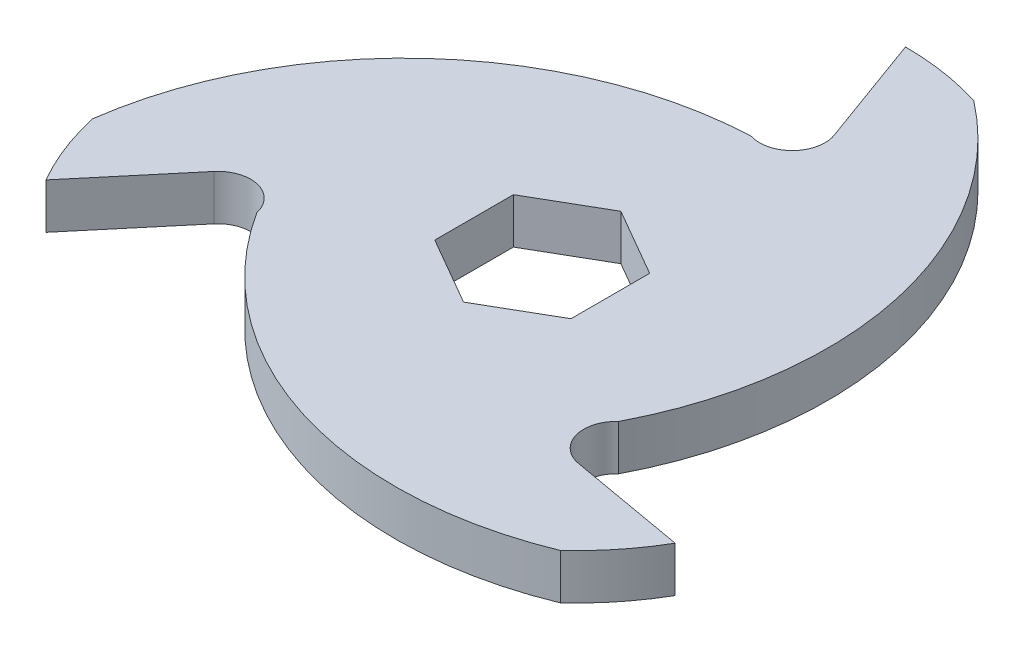
SolidWorks part; units mm, degrees
ref_plane "Front Plane" through (0, 0, 0) normal (0, 0, 1) x (1, 0, 0)
ref_plane "Top Plane" through (0, 0, 0) normal (0, 1, 0) x (1, 0, 0)
ref_plane "Right Plane" through (0, 0, 0) normal (1, 0, 0) x (0, 0, -1)
sketch "Sketch2" plane through (0, 0, 0) normal (0, 1, 0) x (1, 0, 0)
  line L0 (0, 50.8) -> (0, 0) construction
  line L1 (0, 0) -> (-43.9941, -25.4) construction
  line L2 (0, 0) -> (43.9941, -25.4) construction
  line L3 (0, 50.8) -> (5.6992, 35.1416)
  line L4 (43.9941, -25.4) -> (27.5839, -22.5064)
  line L5 (-43.9941, -25.4) -> (-33.2831, -12.6352)
  line L7 (0, 10.9985) -> (-9.525, 5.4993)
  line L8 (-9.525, 5.4993) -> (-9.525, -5.4993)
  line L9 (-9.525, -5.4993) -> (0, -10.9985)
  line L10 (0, -10.9985) -> (9.525, -5.4993)
  line L11 (9.525, -5.4993) -> (9.525, 5.4993)
  line L12 (9.525, 5.4993) -> (0, 10.9985)
  circle A0 centre (0, 0) radius 50.8 construction
  circle A1 centre (0, 13.2055) radius 37.5945
  circle A2 centre (11.4363, -6.6028) radius 37.5945
  circle A3 centre (-11.4363, -6.6028) radius 37.5945
  arc A4 (5.6992, 35.1416) -> (0, 29.21) centre (1.3938, 33.5746) cw
  arc A5 (27.5839, -22.5064) -> (25.2966, -14.605) centre (28.3796, -17.9943) cw
  arc A6 (-33.2831, -12.6352) -> (-25.2966, -14.605) centre (-29.7733, -15.5803) cw
  circle A7 centre (0, 0) radius 9.525 construction
  point P15 (0, 0)
  point P25 (0, 0)
  point P31 (0, 0)
  point P32 (0, 0)
  dimension "D1" = 101.6
  dimension "D4" = 20
  dimension "D2" = 120
  dimension "D3" = 120
  dimension "D5" = 21.59
  dimension "D8" = 19.05
  dimension "D7" = 3
extrude "Boss-Extrude2" add sketch "Sketch2" along normal mid plane 6.35 contours A1 A3 A2 L12 L11 L10 L9 L8 L7 | A1 A6 A2 A3 | L5 A6 A1 A3 | L4 A5 A3 A2 | A3 A5 A1 A2 | A2 A4 A3 A1 | L3 A4 A2 A1
sketch "Sketch3" plane through (0, 3.175, 0) normal (0, 1, 0) x (1, 0, 0)
  line L3 (43.9941, -25.4) -> (27.5839, -22.5064)
  line L4 (0, 50.8) -> (5.6992, 35.1416)
  line L5 (-43.9941, -25.4) -> (-33.2831, -12.6352)
  line L6 (43.9941, -25.4) -> (27.5839, -22.5064)
  line L7 (0, 50.8) -> (5.6992, 35.1416)
  line L8 (-43.9941, -25.4) -> (-33.2831, -12.6352)
  arc A0 (-48.1379, -14.7476) -> (0, 29.21) centre (2.2057, -21.5421) cw
  arc A1 (0, 29.21) -> (-43.9941, -25.4) centre (-11.4363, -6.6028) ccw construction
  arc A2 (0, 29.21) -> (5.6992, 35.1416) centre (1.3938, 33.5746) ccw construction
  arc A3 (11.2972, 49.0624) -> (25.2966, -14.605) centre (-19.7588, 8.8609) cw
  arc A4 (36.8407, -34.3148) -> (-25.2966, -14.605) centre (17.5532, 12.6812) cw
  arc A9 (-25.2966, -14.605) -> (-33.2831, -12.6352) centre (-29.7733, -15.5803) ccw
  arc A10 (-25.2966, -14.605) -> (43.9941, -25.4) centre (11.4363, -6.6028) ccw
  arc A11 (25.2966, -14.605) -> (27.5839, -22.5064) centre (28.3796, -17.9943) ccw
  arc A12 (25.2966, -14.605) -> (0, 50.8) centre (0, 13.2055) ccw
  arc A13 (0, 29.21) -> (5.6992, 35.1416) centre (1.3938, 33.5746) ccw
  arc A14 (0, 29.21) -> (-43.9941, -25.4) centre (-11.4363, -6.6028) ccw
  arc A15 (-25.2966, -14.605) -> (-33.2831, -12.6352) centre (-29.7733, -15.5803) ccw
  arc A16 (-25.2966, -14.605) -> (43.9941, -25.4) centre (11.4363, -6.6028) ccw
  arc A17 (25.2966, -14.605) -> (27.5839, -22.5064) centre (28.3796, -17.9943) ccw
  arc A18 (25.2966, -14.605) -> (0, 50.8) centre (0, 13.2055) ccw
  arc A19 (0, 29.21) -> (5.6992, 35.1416) centre (1.3938, 33.5746) ccw
  arc A20 (0, 29.21) -> (-43.9941, -25.4) centre (-11.4363, -6.6028) ccw
  point P4 (0, 0)
  point P11 (27.5839, -14.605)
  point P26 (0, 0)
  arc M20 (-25.2966, -14.605) -> (43.9941, -25.4) centre (11.4363, -6.6028) ccw
  arc M23 (25.2966, -14.605) -> (0, 50.8) centre (0, 13.2055) ccw
  arc M26 (0, 29.21) -> (-43.9941, -25.4) centre (-11.4363, -6.6028) ccw
  dimension "D3" = 50.8
  dimension "D1" = 11.43
  dimension "D2" = 0
  dimension "D4" = 3
extrude "Cut-Extrude1" cut sketch "Sketch3" against normal through all contours A0 M26 | A3 M23 | A4 M20
